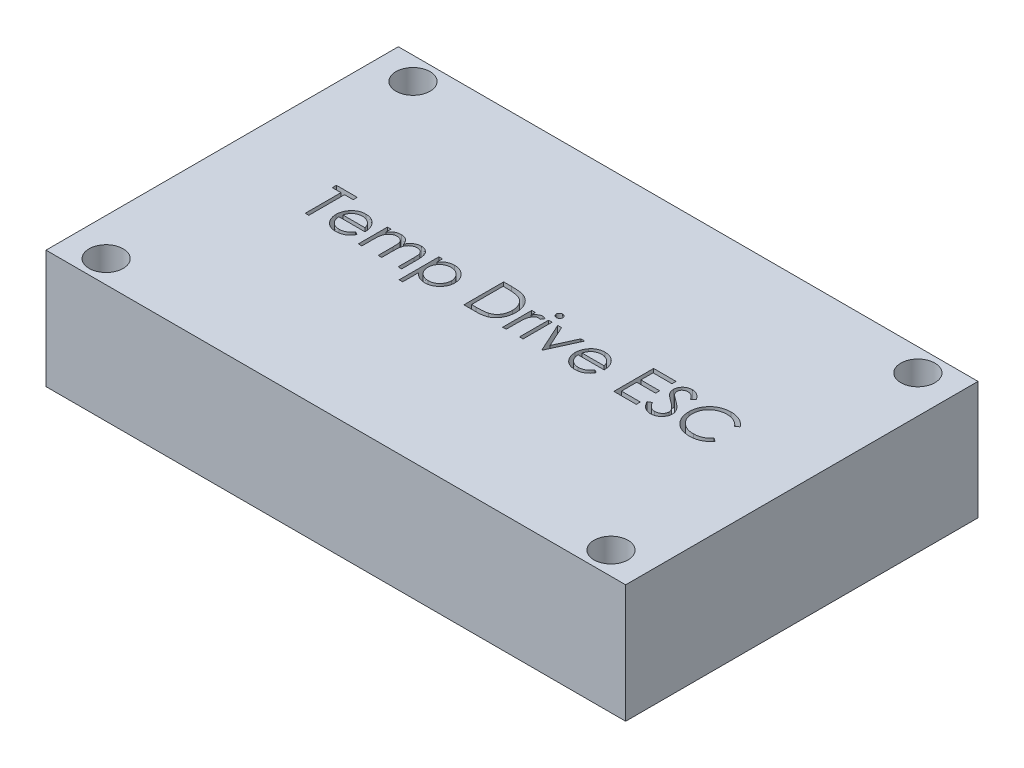
SolidWorks part; units mm, degrees
ref_plane "Front Plane" through (0, 0, 0) normal (0, 0, 1) x (1, 0, 0)
ref_plane "Top Plane" through (0, 0, 0) normal (0, 1, 0) x (1, 0, 0)
ref_plane "Right Plane" through (0, 0, 0) normal (1, 0, 0) x (0, 0, -1)
sketch "Sketch1" plane through (0, 0, 0) normal (0, 1, 0) x (1, 0, 0)
  line L0 (-22.2097, 13.5) -> (-22.2097, -13.5) construction
  line L1 (-25.5, -15.5) -> (25.5, -15.5)
  line L2 (-25.5, -15.5) -> (-25.5, 15.5)
  line L3 (-25.5, 15.5) -> (25.5, 15.5)
  line L4 (25.5, -15.5) -> (25.5, 15.5)
  line L5 (-25.5, -15.5) -> (25.5, 15.5) construction
  line L6 (-25.5, 15.5) -> (25.5, -15.5) construction
  line L7 (-22.2097, -13.5) -> (22.2097, -13.5) construction
  line L8 (22.2097, -13.5) -> (22.2097, 13.5) construction
  line L9 (22.2097, 13.5) -> (-22.2097, 13.5) construction
  circle A0 centre (-22.2097, 13.5) radius 1.5
  circle A1 centre (22.2097, 13.5) radius 1.5
  circle A2 centre (22.2097, -13.5) radius 1.5
  circle A3 centre (-22.2097, -13.5) radius 1.5
  point P0 (0, 0)
  point P16 (-22.3154, -13.5)
  dimension "D3" = 3
  dimension "D4" = 3
  dimension "D5" = 3
  dimension "D6" = 3
  dimension "D1" = 51
  dimension "D2" = 31
  dimension "D7" = 2
  dimension "D8" = 2
  dimension "D9" = 2
  dimension "D10" = 2
  dimension "D11" = 44.4194
  dimension "D12" = 27
extrude "Boss-Extrude1" add sketch "Sketch1" along normal blind 10.4
sketch "Sketch2" plane through (0, 10.4, 0) normal (0, 1, 0) x (1, 0, 0)
  text T0 "Temp Drive ESC"
extrude "Cut-Extrude1" cut sketch "Sketch2" against normal blind 1.4
